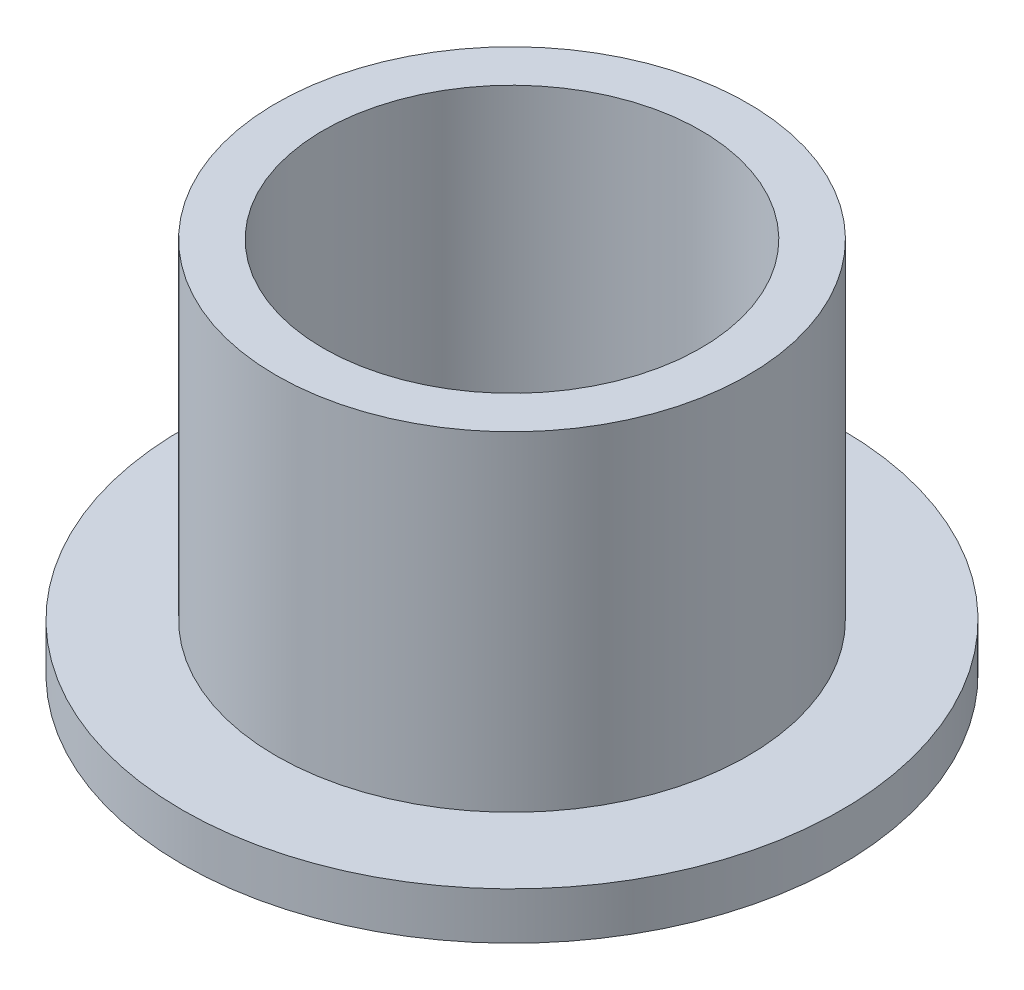
SolidWorks part; units mm, degrees
ref_plane "Front" through (0, 0, 0) normal (0, 0, 1) x (1, 0, 0)
ref_plane "Top" through (0, 0, 0) normal (0, 1, 0) x (1, 0, 0)
ref_plane "Right" through (0, 0, 0) normal (1, 0, 0) x (0, 0, -1)
sketch "Sketch1" plane through (0, 0, 0) normal (0, 1, 0) x (1, 0, 0)
  circle A0 centre (0, 0) radius 6.3627
  circle A1 centre (0, 0) radius 7.9502
  circle A2 centre (0, 0) radius 11.1125
  dimension "ID" = 12.7254
  dimension "OD" = 15.9004
  dimension "FlangeOD" = 22.225
sketch "Sketch2" plane through (0, 0, 0) normal (0, 1, 0) x (1, 0, 0)
  circle A0 centre (0, 0) radius 6.3627 construction
  circle A1 centre (0, 0) radius 7.9502 construction
  circle A2 centre (0, 0) radius 6.3627
  circle A3 centre (0, 0) radius 7.9502
extrude "Boss-Extrude1" add sketch "Sketch2" along normal blind 12.7
sketch "Sketch3" plane through (0, 0, 0) normal (0, 1, 0) x (1, 0, 0)
  circle A0 centre (0, 0) radius 11.1125 construction
  circle A1 centre (0, 0) radius 7.9502 construction
  circle A2 centre (0, 0) radius 11.1125
  circle A3 centre (0, 0) radius 7.9502
extrude "Boss-Extrude2" add sketch "Sketch3" along normal blind 1.5875
